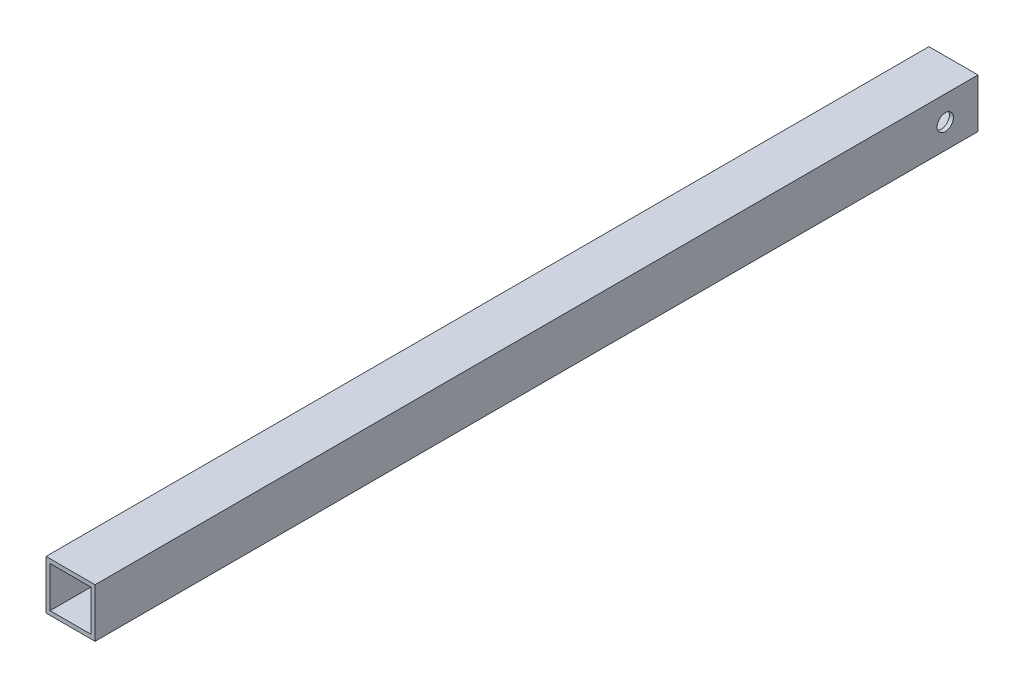
SolidWorks part; units mm, degrees
ref_plane "Front Plane" through (0, 0, 0) normal (0, 0, 1) x (1, 0, 0)
ref_plane "Top Plane" through (0, 0, 0) normal (0, 1, 0) x (1, 0, 0)
ref_plane "Right Plane" through (0, 0, 0) normal (1, 0, 0) x (0, 0, -1)
sketch "Sketch1" plane through (0, 0, 0) normal (0, 0, 1) x (1, 0, 0)
  line L1 (-38.1, -38.1) -> (38.1, -38.1)
  line L2 (-38.1, -38.1) -> (-38.1, 38.1)
  line L3 (-38.1, 38.1) -> (38.1, 38.1)
  line L4 (38.1, -38.1) -> (38.1, 38.1)
  line L5 (-38.1, -38.1) -> (38.1, 38.1) construction
  line L6 (-38.1, 38.1) -> (38.1, -38.1) construction
  line L7 (-31.75, -31.75) -> (31.75, -31.75)
  line L8 (-31.75, -31.75) -> (-31.75, 31.75)
  line L9 (-31.75, 31.75) -> (31.75, 31.75)
  line L10 (31.75, -31.75) -> (31.75, 31.75)
  line L11 (-31.75, -31.75) -> (31.75, 31.75) construction
  line L12 (-31.75, 31.75) -> (31.75, -31.75) construction
  point P0 (0, 0)
  point P6 (0, 0)
  dimension "D1" = 6.35
  dimension "D2" = 76.2
extrude "Boss-Extrude1" add sketch "Sketch1" along normal blind 1371.6
sketch "Sketch2" plane through (38.1, 0, 0) normal (1, 0, 0) x (0, 0, -1)
  line L0 (0, 0) -> (-50.8, 0) construction
  line L1 (0, -38.1) -> (0, 38.1) construction
  circle A0 centre (-50.8, 0) radius 12.7
  dimension "D1" = 25.4
  dimension "D2" = 50.8
extrude "Cut-Extrude1" cut sketch "Sketch2" against normal through all
